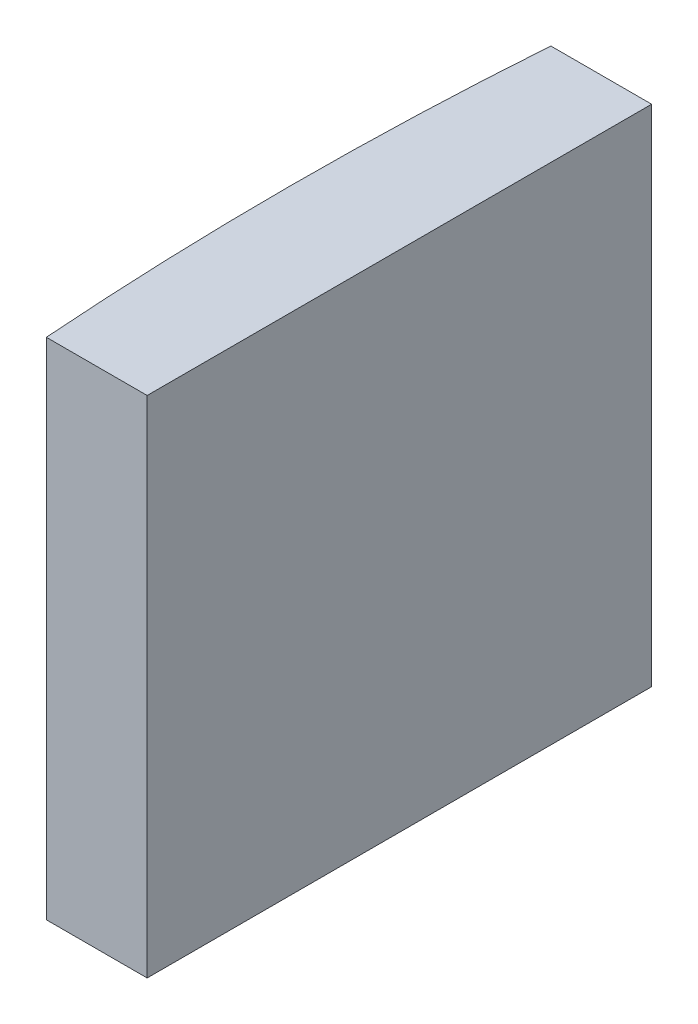
SolidWorks part; units mm, degrees
ref_plane "前视基准面" through (0, 0, 0) normal (0, 0, 1) x (1, 0, 0)
ref_plane "上视基准面" through (0, 0, 0) normal (0, 1, 0) x (1, 0, 0)
ref_plane "右视基准面" through (0, 0, 0) normal (1, 0, 0) x (0, 0, -1)
sketch "草图1" plane through (0, 0, 0) normal (0, 1, 0) x (1, 0, 0)
  line L0 (-77.0643, 0) -> (10.8051, 0) construction
  line L1 (-64.2428, 5) -> (-62.2448, 5)
  line L2 (-64.2428, -5) -> (-62.2448, -5)
  line L3 (-62.2448, 5) -> (-62.2448, -5)
  arc A0 (-64.2428, 5) -> (-64.2428, -5) centre (4.3552, 0) ccw
  point P2 (-64.4248, 0)
  point P4 (-62.2448, 0)
  point P8 (-77.0643, 0)
  dimension "D2" = 5
  dimension "D3" = 68.78
  dimension "D4" = 2.18
  dimension "D1" = 5
extrude "凸台-拉伸1" add sketch "草图1" along normal blind 10
